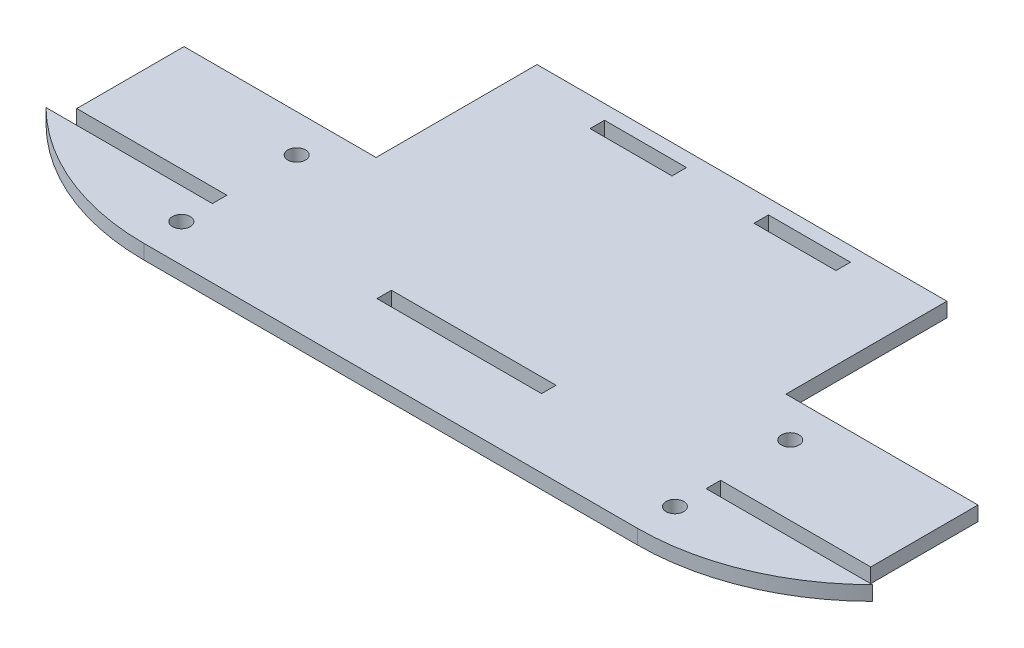
SolidWorks part; units mm, degrees
ref_plane "Ön Düzlem" through (0, 0, 0) normal (0, 0, 1) x (1, 0, 0)
ref_plane "Üst Düzlem" through (0, 0, 0) normal (0, 1, 0) x (1, 0, 0)
ref_plane "Sağ Düzlem" through (0, 0, 0) normal (1, 0, 0) x (0, 0, -1)
sketch "Sketch1" plane through (0, 0, 0) normal (0, 1, 0) x (1, 0, 0)
  line L1 (-46, 0) -> (46, 0)
  line L19 (-73.9952, 35.5) -> (-73.9952, 15.5)
  line L21 (73.9952, 35.5) -> (73.9952, 15.5)
  line L22 (-15.34, 15.5) -> (-15.34, 12.8)
  line L23 (-46.0152, 15.5) -> (-46.0152, 12.8)
  line L24 (-15.34, 12.8) -> (15.34, 12.8)
  line L25 (15.34, 12.8) -> (15.34, 15.5)
  line L26 (15.34, 15.5) -> (-15.34, 15.5)
  line L29 (46.0152, 15.5) -> (46.0152, 12.8)
  line L31 (46.0152, 15.5) -> (73.9952, 15.5)
  line L32 (77.0252, 12.8) -> (46.0152, 12.8)
  line L33 (-46.0152, 15.5) -> (-73.9952, 15.5)
  line L34 (-46.0152, 12.8) -> (-77.0252, 12.8)
  line L35 (-73.9952, 35.5) -> (-38.2, 35.5)
  line L37 (73.9952, 35.5) -> (38.2, 35.5)
  line L39 (-38.2, 65.5) -> (38.2, 65.5)
  line L41 (-38.2, 65.5) -> (-38.2, 35.5)
  line L42 (38.2, 35.5) -> (38.2, 65.5)
  line L45 (-22.92, 62.8) -> (-7.64, 62.8)
  line L47 (7.64, 62.8) -> (22.92, 62.8)
  line L49 (22.92, 60.1) -> (7.64, 60.1)
  line L51 (-7.64, 60.1) -> (-22.92, 60.1)
  line L53 (-22.92, 62.8) -> (-22.92, 60.1)
  line L54 (-7.64, 62.8) -> (-7.64, 60.1)
  line L55 (7.64, 62.8) -> (7.64, 60.1)
  line L56 (22.92, 62.8) -> (22.92, 60.1)
  arc A0 (-77.0252, 12.8) -> (-46, 0) centre (-46, 44) ccw
  arc A1 (46, 0) -> (77.0252, 12.8) centre (46, 44) ccw
  circle A2 centre (46, 28.5) radius 1.65
  circle A3 centre (46, 7) radius 1.65
  circle A4 centre (-46, 7) radius 1.65
  circle A5 centre (-46, 28.5) radius 1.65
extrude "Boss-Extrude1" add sketch "Sketch1" along normal blind 2.7
